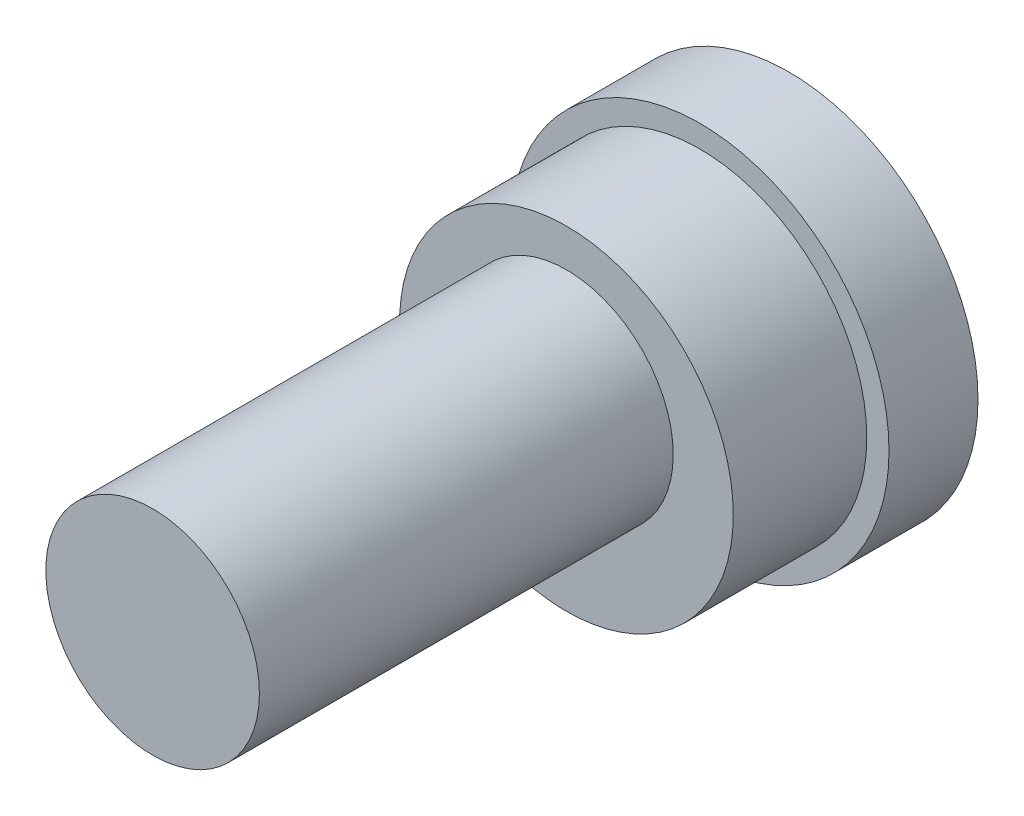
SolidWorks part; units mm, degrees
ref_plane "正面" through (0, 0, 0) normal (0, 0, 1) x (1, 0, 0)
ref_plane "平面" through (0, 0, 0) normal (0, 1, 0) x (1, 0, 0)
ref_plane "右側面" through (0, 0, 0) normal (1, 0, 0) x (0, 0, -1)
sketch "ｽｹｯﾁ1" plane through (0, 0, 0) normal (0, 0, 1) x (1, 0, 0)
  circle A0 centre (0, 0) radius 42.5
  dimension "D1" = 85
extrude "ﾎﾞｽ - 押し出し1" add sketch "ｽｹｯﾁ1" along normal blind 20
sketch "ｽｹｯﾁ2" plane through (0, 0, 20) normal (0, 0, 1) x (1, 0, 0)
  circle A0 centre (0, 0) radius 37.5
  dimension "D1" = 75
extrude "ﾎﾞｽ - 押し出し2" add sketch "ｽｹｯﾁ2" along normal blind 30
sketch "ｽｹｯﾁ3" plane through (0, 0, 50) normal (0, 0, 1) x (1, 0, 0)
  line L0 (0, 5) -> (0, 0) construction
  line L1 (0, 29) -> (0, 37.5) construction
  circle A0 centre (0, 5) radius 24
  circle A1 centre (0, 0) radius 37.5 construction
  dimension "D2" = 48
  dimension "D1" = 8.5
extrude "ﾎﾞｽ - 押し出し3" add sketch "ｽｹｯﾁ3" along normal blind 93
sketch "ｽｹｯﾁ5" plane through (0, 0, 143) normal (0, 0, 1) x (1, 0, 0)
  circle A0 centre (0, 5) radius 20
  circle A1 centre (0, 5) radius 24 construction
  dimension "D1" = 40
sketch "ｽｹｯﾁ21" plane through (0, 0, 0) normal (0, 0, -1) x (-1, 0, 0)
  point P0 (0, 0)
sketch3d "3Dｽｹｯﾁ1"
  line L0 (0, 0, 0) -> (0, 30, 0)
  line L1 (0, 0, 0) -> (-30, 0, 0)
  line L2 (0, 0, 0) -> (0, 0, 30)
  dimension "D1" = 30
  dimension "D2" = 30
  dimension "D3" = 30
